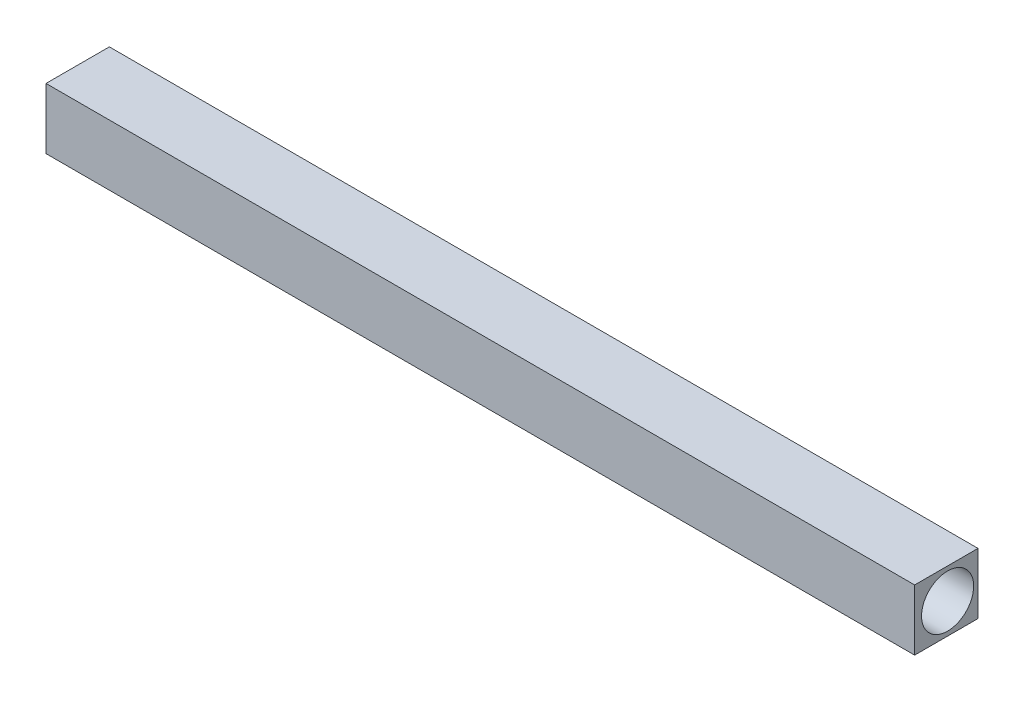
SolidWorks part; units mm, degrees
material "Malleable Cast Iron"
ref_plane "Front Plane" through (0, 0, 0) normal (0, 0, 1) x (1, 0, 0)
ref_plane "Top Plane" through (0, 0, 0) normal (0, 1, 0) x (1, 0, 0)
ref_plane "Right Plane" through (0, 0, 0) normal (1, 0, 0) x (0, 0, -1)
sketch "Sketch1" plane through (0, 0, 0) normal (0, 1, 0) x (1, 0, 0)
  line L1 (-59.3425, 0) -> (440.6575, 0)
  line L2 (-59.3425, 0) -> (-59.3425, -36.4583)
  line L3 (-59.3425, -36.4583) -> (440.6575, -36.4583)
  line L4 (440.6575, 0) -> (440.6575, -36.4583)
  dimension "D1" = 500
extrude "Boss-Extrude1" add sketch "Sketch1" along normal blind 35
sketch "Sketch2" plane through (440.6575, 0, 0) normal (1, 0, 0) x (0, 0, -1)
  circle A0 centre (-17.5, 17.5) radius 15
  dimension "D1" = 30
extrude "Cut-Extrude1" cut sketch "Sketch2" against normal through all
